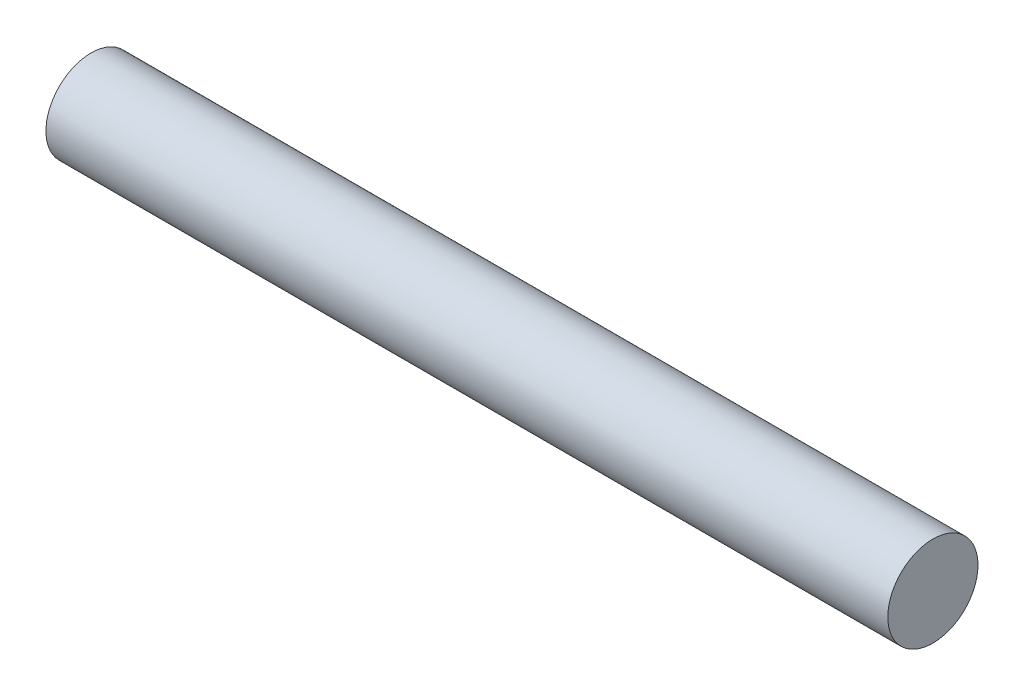
SolidWorks part; units mm, degrees
ref_plane "Front Plane" through (0, 0, 0) normal (0, 0, 1) x (1, 0, 0)
ref_plane "Top Plane" through (0, 0, 0) normal (0, 1, 0) x (1, 0, 0)
ref_plane "Right Plane" through (0, 0, 0) normal (1, 0, 0) x (0, 0, -1)
sketch "Sketch1" plane through (0, 0, 0) normal (1, 0, 0) x (0, 0, -1)
  circle A0 centre (0, 0) radius 1.5
  dimension "D1" = 3
extrude "Boss-Extrude1" add sketch "Sketch1" along normal mid plane 28
